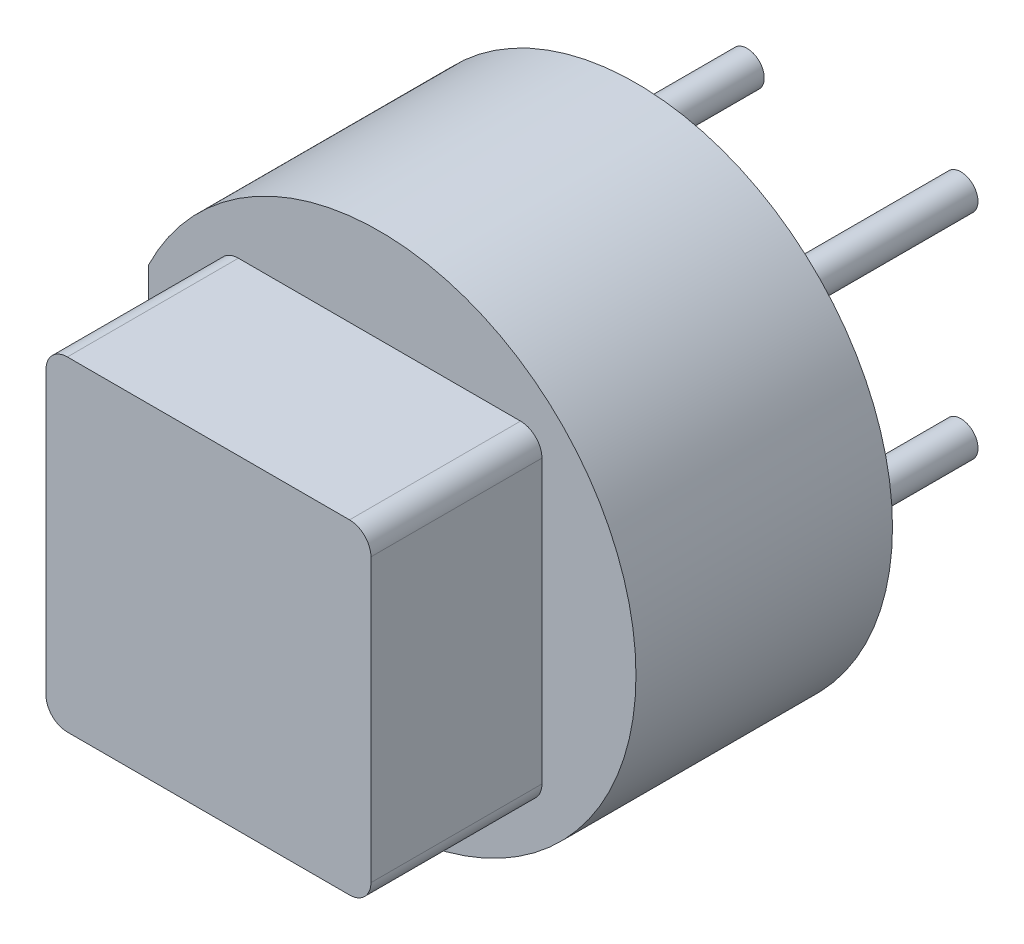
SolidWorks part; units mm, degrees
ref_plane "Plan de face" through (0, 0, 0) normal (0, 0, 1) x (1, 0, 0)
ref_plane "Plan de dessus" through (0, 0, 0) normal (0, 1, 0) x (1, 0, 0)
ref_plane "Plan de droite" through (0, 0, 0) normal (1, 0, 0) x (0, 0, -1)
sketch "Esquisse1" plane through (0, 0, 0) normal (0, 0, 1) x (1, 0, 0)
  line L0 (-5.4, 2.6153) -> (-5.4, -2.6153)
  arc A0 (-5.4, 2.6153) -> (-5.4, -2.6153) centre (0, 0) cw
  dimension "D1" = 6
  dimension "D2" = 5.4
extrude "Boss.-Extru.1" add sketch "Esquisse1" along normal blind 6
sketch "Esquisse2" plane through (0, 0, 6) normal (0, 0, 1) x (1, 0, 0)
  line L1 (-3.8, -3.8) -> (3.8, -3.8)
  line L2 (-3.8, -3.8) -> (-3.8, 3.8)
  line L3 (-3.8, 3.8) -> (3.8, 3.8)
  line L4 (3.8, -3.8) -> (3.8, 3.8)
  line L5 (-3.8, -3.8) -> (3.8, 3.8) construction
  line L6 (-3.8, 3.8) -> (3.8, -3.8) construction
  point P0 (0, 0)
  dimension "D1" = 7.6
extrude "Boss.-Extru.2" add sketch "Esquisse2" along normal blind 4
sketch "Esquisse3" plane through (0, 0, 0) normal (0, 0, -1) x (-1, 0, 0)
  line L0 (4.8, -2.4739) -> (4.8, 2.4739)
  line L1 (5.4, 2.6153) -> (5.4, -2.6153) construction
  arc A0 (4.8, -2.4739) -> (4.8, 2.4739) centre (0, 0) cw
  point P6 (4.6, -1.4804)
  dimension "D2" = 5.4
  dimension "D1" = 0.6
extrude "Enlèv. mat.-Extru.1" cut sketch "Esquisse3" against normal blind 0.1
sketch "Esquisse4" plane through (0, 0, 0.1) normal (0, 0, -1) x (-1, 0, 0)
  line L0 (0, -4) -> (0, 0) construction
  line L1 (0, 0) -> (0, 4) construction
  line L2 (4, 0) -> (0, 0) construction
  line L3 (0, 0) -> (-4, 0) construction
  circle A0 centre (0, 0) radius 1.5
  circle A1 centre (0, -4) radius 0.6
  circle A2 centre (-4, 0) radius 0.6
  circle A3 centre (0, 4) radius 0.6
  circle A4 centre (4, 0) radius 0.6
  dimension "D1" = 3
  dimension "D2" = 1.2
  dimension "D3" = 4
extrude "Boss.-Extru.4" add sketch "Esquisse4" along normal blind 1.2
sketch "Esquisse5" plane through (0, 0, 0.1) normal (0, 0, -1) x (-1, 0, 0)
  line L1 (-2.5, 2.5) -> (2.5, 2.5) construction
  line L2 (-2.5, 2.5) -> (-2.5, -2.5) construction
  line L3 (-2.5, -2.5) -> (2.5, -2.5) construction
  line L4 (2.5, 2.5) -> (2.5, -2.5) construction
  line L5 (-2.5, 2.5) -> (2.5, -2.5) construction
  line L6 (-2.5, -2.5) -> (2.5, 2.5) construction
  circle A0 centre (2.5, -2.5) radius 0.4
  circle A1 centre (-2.5, -2.5) radius 0.4
  circle A2 centre (-2.5, 2.5) radius 0.4
  circle A3 centre (2.5, 2.5) radius 0.4
  point P0 (0, 0)
  dimension "D2" = 0.8
  dimension "D1" = 5
extrude "Boss.-Extru.5" add sketch "Esquisse5" along normal blind 5.2
fillet "Congé1" radius 0.5 4 edges at (-3.8, -3.8, 8) (-3.8, 3.8, 8) (3.8, 3.8, 8) (3.8, -3.8, 8)
